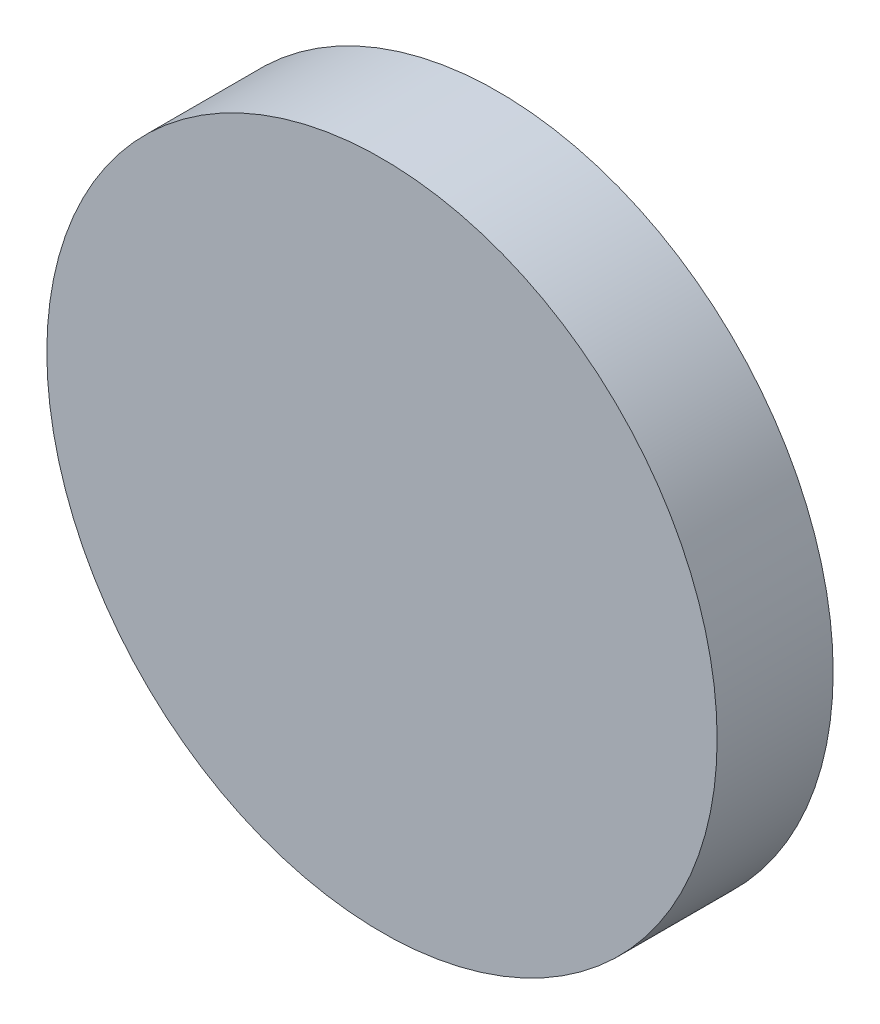
SolidWorks part; units mm, degrees
ref_plane "Front Plane" through (0, 0, 0) normal (0, 0, 1) x (1, 0, 0)
ref_plane "Top Plane" through (0, 0, 0) normal (0, 1, 0) x (1, 0, 0)
ref_plane "Right Plane" through (0, 0, 0) normal (1, 0, 0) x (0, 0, -1)
sketch "Sketch1" plane through (0, 0, 0) normal (0, 0, 1) x (1, 0, 0)
  circle A0 centre (0, 0) radius 65
  dimension "D1" = 130
extrude "Boss-Extrude1" add sketch "Sketch1" along normal blind 22.5 contours A0
scale "Scale1" scale about centroid uniform scaling yes scale factor 50
